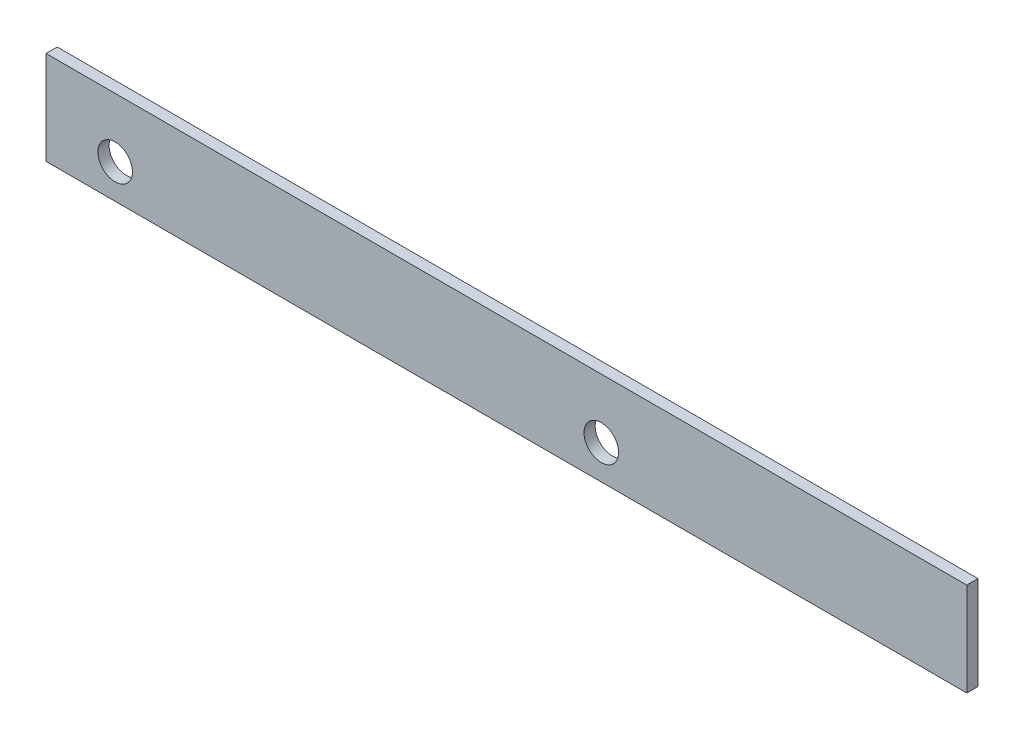
SolidWorks part; units mm, degrees
ref_plane "Alzado" through (0, 0, 0) normal (0, 0, 1) x (1, 0, 0)
ref_plane "Planta" through (0, 0, 0) normal (0, 1, 0) x (1, 0, 0)
ref_plane "Vista lateral" through (0, 0, 0) normal (1, 0, 0) x (0, 0, -1)
sketch "Croquis1" plane through (0, 0, 0) normal (0, 0, 1) x (1, 0, 0)
  line L0 (0, 0) -> (0, 100)
  line L1 (0, 100) -> (985, 100)
  line L2 (985, 100) -> (985, 0)
  line L3 (985, 0) -> (0, 0)
  dimension "D1" = 985
  dimension "D2" = 100
extrude "Saliente-Extruir1" add sketch "Croquis1" along normal blind 12
sketch "Croquis2" plane through (0, 0, 12) normal (0, 0, 1) x (1, 0, 0)
  line L0 (74, 0) -> (74, 36.5) construction
  line L1 (0, 0) -> (985, 0) construction
  line L2 (74, 36.5) -> (0, 36.5) construction
  line L3 (0, 100) -> (0, 0) construction
  circle A0 centre (74, 36.5) radius 18.5
  dimension "D1" = 74
  dimension "D2" = 36.5
extrude "Cortar-Extruir1" cut sketch "Croquis2" against normal through all and the other way through all
sketch "Croquis3" plane through (0, 0, 12) normal (0, 0, 1) x (1, 0, 0)
  line L0 (594, 0) -> (594, 36.5) construction
  line L1 (0, 0) -> (985, 0) construction
  line L2 (594, 36.5) -> (985, 36.5) construction
  line L3 (985, 0) -> (985, 100) construction
  circle A0 centre (594, 36.5) radius 18.5
  dimension "D1" = 391
  dimension "D2" = 36.5
extrude "Cortar-Extruir2" cut sketch "Croquis3" against normal through all
